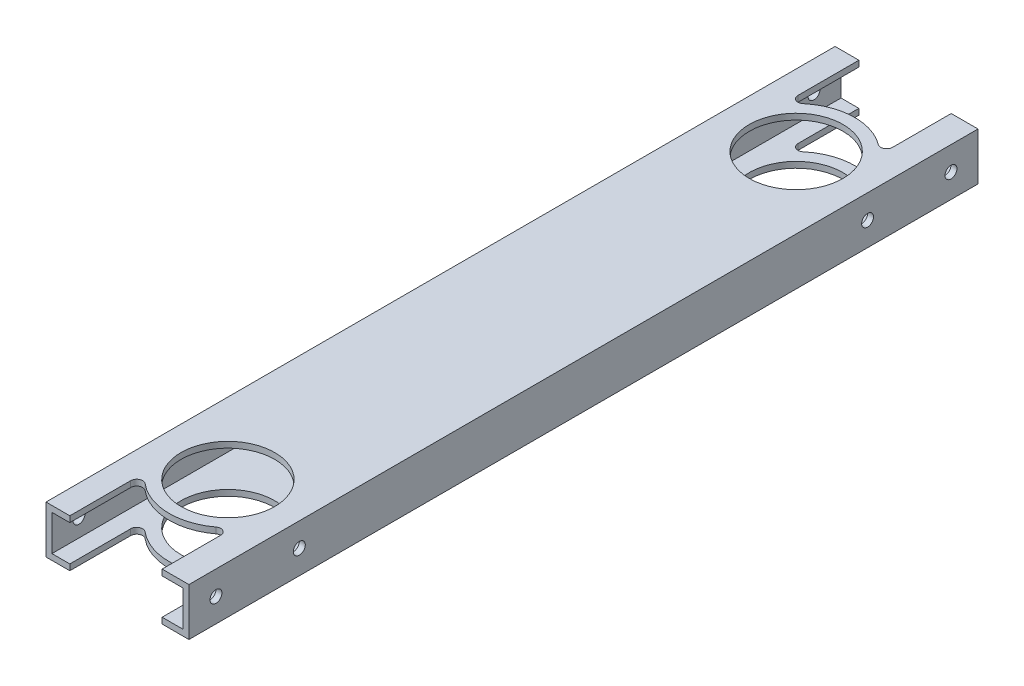
SolidWorks part; units mm, degrees
ref_plane "Front" through (0, 0, 0) normal (0, 0, 1) x (1, 0, 0)
ref_plane "Top" through (0, 0, 0) normal (0, 1, 0) x (1, 0, 0)
ref_plane "Right" through (0, 0, 0) normal (1, 0, 0) x (0, 0, -1)
sketch "Sketch1" plane through (0, 0, 0) normal (0, 0, 1) x (1, 0, 0)
  line L1 (-38.1, -12.7) -> (38.1, -12.7)
  line L2 (-38.1, -12.7) -> (-38.1, 12.7)
  line L3 (-38.1, 12.7) -> (38.1, 12.7)
  line L4 (38.1, -12.7) -> (38.1, 12.7)
  line L5 (-38.1, -12.7) -> (38.1, 12.7) construction
  line L6 (-38.1, 12.7) -> (38.1, -12.7) construction
  point P0 (0, 0)
  dimension "D1" = 25.4
  dimension "D2" = 76.2
extrude "Extrude-Thin1" add sketch "Sketch1" along normal blind 420.6926 thin thin type one direction reverse wall 3.175
ref_plane "Plane3" through (0, 0, 0) normal (0, 0, -1) x (-1, 0, 0)
sketch "Sketch4" plane through (0, 12.7, 0) normal (0, 1, 0) x (1, 0, 0)
  line L0 (0, -58.8645) -> (0, -361.8281) construction
  line L1 (-38.1, -420.6926) -> (-38.1, 0) construction
  line L2 (0, -58.8645) -> (0, -361.8281) construction
  circle A0 centre (0, -361.8281) radius 24.972
  circle A1 centre (0, -58.8645) radius 24.972
  point P4 (0, 0)
  point P5 (0, -350.4423)
  point P6 (0, -48.9317)
  point P7 (0, 0)
  point P10 (-38.1, -210.3463)
  point P11 (0, -91.6999)
  point P14 (0, -210.3463)
  point P15 (0, 0)
  point P16 (24.972, -58.8645)
  point P21 (0, -358.9523)
  dimension "D1" = 49.944
  dimension "D2" = 302.9636
extrude "Cut-Extrude3" cut sketch "Sketch4" against normal through all
sketch "Sketch6" plane through (0, 12.7, 0) normal (0, 1, 0) x (1, 0, 0)
  line L1 (-38.1, -210.3463) -> (38.1, -210.3463) construction
  line L3 (-38.1, -420.6926) -> (-38.1, 0) construction
  line L8 (-25.4, 0) -> (-25.4, -40.5367)
  line L10 (-38.1, -420.6926) -> (-38.1, 0) construction
  line L12 (23.8125, -38.5167) -> (23.8125, 0)
  line L19 (38.1, -420.6926) -> (38.1, 0) construction
  line L20 (38.1, 0) -> (-38.1, 0) construction
  line L23 (-25.4, 0) -> (23.8125, 0)
  arc A0 (23.8125, -31.2215) -> (18.7381, -33.7656) centre (20.6375, -31.2215) cw
  arc A1 (-25.4, -32.4809) -> (-20.1795, -34.9092) centre (-22.225, -32.4809) ccw
  circle A4 centre (0, -58.8645) radius 31.322
  circle A6 centre (0, -58.8645) radius 24.972 construction
  line M63 (38.1, 0) -> (-38.1, 0)
  dimension "D5" = 3.175
  dimension "D6" = 3.175
  dimension "D3" = 6.35
  dimension "D1" = 12.7
  dimension "D2" = 14.2875
extrude "Cut-Extrude7" cut sketch "Sketch6" against normal through all contours A4 A0 L12 L8 A1 M63
sketch "Sketch7" plane through (38.1, 0, 0) normal (1, 0, 0) x (0, 0, -1)
  line L0 (0, 0) -> (-14.4145, 0) construction
  circle A0 centre (-14.4145, 0) radius 3.175
  dimension "D1" = 6.35
  dimension "D2" = 14.4145
extrude "Cut-Extrude8" cut sketch "Sketch7" against normal through all
ref_plane "Plane2" through (0, 0, 210.3463) normal (0, 0, 1) x (1, 0, 0)
mirror "Mirror3" about plane through (0, 0, 210.3463) normal (0, 0, 1) of "Cut-Extrude8", "Cut-Extrude7"
sketch "Sketch8" plane through (38.1, 0, 0) normal (1, 0, 0) x (0, 0, -1)
  line L0 (0, 0) -> (-58.8645, 0) construction
  line L2 (-210.3463, 12.7) -> (-210.3463, -12.7) construction
  line L3 (-420.6926, 12.7) -> (0, 12.7) construction
  line L4 (-420.6926, -12.7) -> (0, -12.7) construction
  line L5 (-33.8925, 12.7) -> (-83.8365, 12.7) construction
  line L6 (-33.8925, 12.7) -> (-83.8365, 12.7) construction
  line L7 (-58.8645, 12.7) -> (-58.8645, 0) construction
  circle A0 centre (-58.8645, 0) radius 3.175
  circle A1 centre (-361.8281, 0) radius 3.175
  point P2 (0, 0)
  dimension "D2" = 6.35
extrude "Cut-Extrude9" cut sketch "Sketch8" against normal through all
